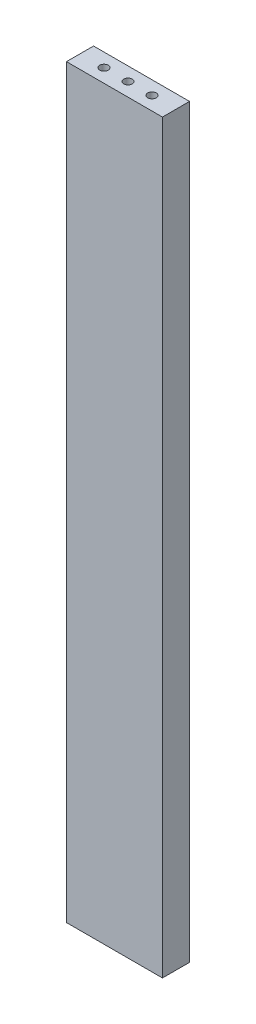
SolidWorks part; units mm, degrees
material "Pino"
ref_plane "Alzado" through (0, 0, 0) normal (0, 0, 1) x (1, 0, 0)
ref_plane "Planta" through (0, 0, 0) normal (0, 1, 0) x (1, 0, 0)
ref_plane "Vista lateral" through (0, 0, 0) normal (1, 0, 0) x (0, 0, -1)
sketch "Croquis1" plane through (0, 0, 0) normal (0, 1, 0) x (1, 0, 0)
  line L1 (-45, 12.7) -> (45, 12.7)
  line L2 (-45, 12.7) -> (-45, -12.7)
  line L3 (-45, -12.7) -> (45, -12.7)
  line L4 (45, 12.7) -> (45, -12.7)
  line L5 (-45, 12.7) -> (45, -12.7) construction
  line L6 (-45, -12.7) -> (45, 12.7) construction
  point P0 (0, 0)
  dimension "D1" = 90
  dimension "D2" = 25.4
extrude "Saliente-Extruir1" add sketch "Croquis1" along normal blind 699.2
sketch "Croquis3" plane through (0, 699.2, 0) normal (0, 1, 0) x (1, 0, 0)
  circle A0 centre (0, 0) radius 4
  circle A1 centre (22.5, 0) radius 4
  circle A2 centre (-22.5, 0) radius 4
  dimension "D1" = 8
  dimension "D2" = 22.5
  dimension "D3" = 22.5
extrude "Cortar-Extruir1" cut sketch "Croquis3" against normal blind 10
sketch "Croquis4" plane through (0, 0, 0) normal (0, -1, 0) x (1, 0, 0)
  circle A0 centre (0, 0) radius 4
  circle A1 centre (22.5, 0) radius 4
  circle A2 centre (-22.5, 0) radius 4
  circle A3 centre (0, 0) radius 4 construction
  circle A4 centre (22.5, 0) radius 4 construction
  circle A5 centre (-22.5, 0) radius 4 construction
extrude "Cortar-Extruir2" cut sketch "Croquis4" against normal blind 10
